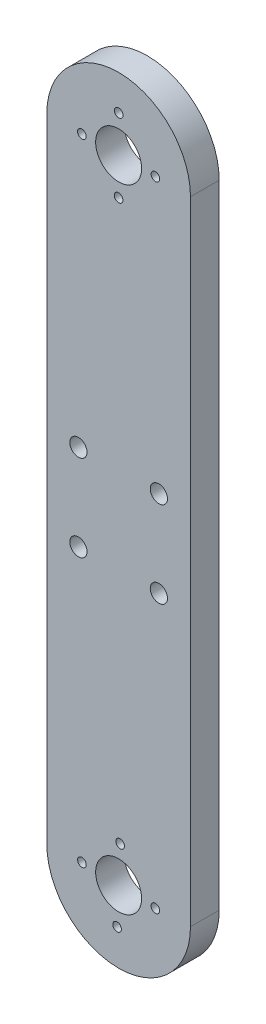
SolidWorks part; units mm, degrees
material "Acrylic (Medium-high impact)"
ref_plane "Front Plane" through (0, 0, 0) normal (0, 0, 1) x (1, 0, 0)
ref_plane "Top Plane" through (0, 0, 0) normal (0, 1, 0) x (1, 0, 0)
ref_plane "Right Plane" through (0, 0, 0) normal (1, 0, 0) x (0, 0, -1)
sketch "Sketch2" plane through (0, 0, 0) normal (0, 0, 1) x (1, 0, 0)
  line L0 (0, 0) -> (0, -110) construction
  line L1 (12.5, 0) -> (12.5, -110)
  line L2 (-12.5, 0) -> (-12.5, -110)
  arc A0 (12.5, 0) -> (-12.5, 0) centre (0, 0) ccw
  arc A1 (-12.5, -110) -> (12.5, -110) centre (0, -110) ccw
  circle A2 centre (0, 0) radius 4
  circle A4 centre (0, -110) radius 4
  circle A5 centre (7, -47.5) radius 1.5
  circle A6 centre (-7, -47.5) radius 1.5
  circle A7 centre (7, -62.5) radius 1.5
  circle A8 centre (-7, -62.5) radius 1.5
  circle A18 centre (6.391, -110.2662) radius 0.75
  circle A19 centre (-0.2662, -116.391) radius 0.75
  circle A20 centre (-6.391, -109.7338) radius 0.75
  circle A21 centre (0.2662, -103.609) radius 0.75
  circle A22 centre (-6.3965, 0.009) radius 0.75
  circle A23 centre (0.009, 6.3965) radius 0.75
  circle A24 centre (-0.009, -6.3965) radius 0.75
  circle A25 centre (6.3965, -0.009) radius 0.75
  point P3 (0, -55)
  dimension "D2" = 8
  dimension "D3" = 12.5
  dimension "D4" = 8
  dimension "D5" = 7
  dimension "D7" = 3
  dimension "D8" = 3
  dimension "D13" = 3
  dimension "D14" = 3
  dimension "D1" = 110
  dimension "D6" = 47.5
  dimension "D9" = 7
  dimension "D10" = 47.5
  dimension "D11" = 7
  dimension "D12" = 7
  dimension "D15" = 47.5
  dimension "D16" = 47.5
extrude "Boss-Extrude1" add sketch "Sketch2" along normal blind 5
